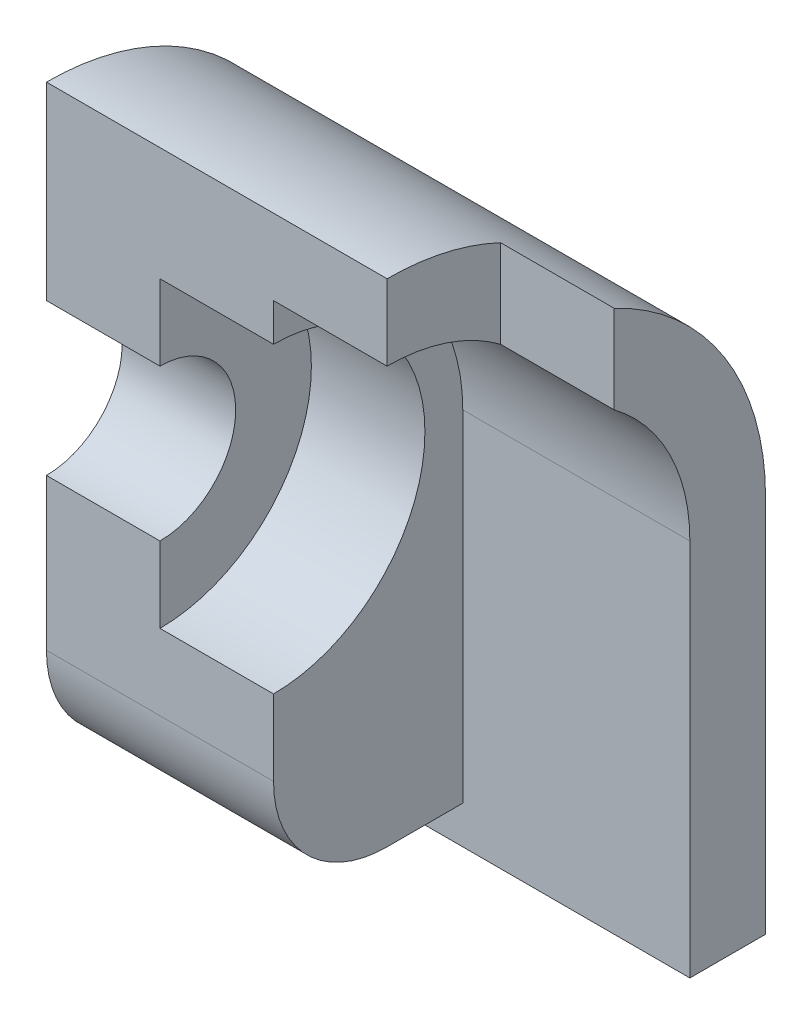
SolidWorks part; units mm, degrees
ref_plane "Front" through (0, 0, 0) normal (0, 0, 1) x (1, 0, 0)
ref_plane "Top" through (0, 0, 0) normal (0, 1, 0) x (1, 0, 0)
ref_plane "Right" through (0, 0, 0) normal (1, 0, 0) x (0, 0, -1)
sketch "Sketch1" plane through (0, 0, 0) normal (1, 0, 0) x (0, 0, -1)
  line L1 (3.5, -8) -> (-0.5, -8)
  line L2 (3.5, -8) -> (3.5, 8)
  line L3 (3.5, 8) -> (-3.5, 8)
  line L4 (-3.5, -5) -> (-3.5, 8)
  line L5 (3.5, -8) -> (-3.5, 8) construction
  line L6 (3.5, 8) -> (-3.5, -8) construction
  line L7 (3.5, -8) -> (1.5, -8)
  line L8 (3.5, -8) -> (3.5, -9)
  line L9 (3.5, -9) -> (1.5, -9)
  line L10 (1.5, -8) -> (1.5, -9)
  arc A0 (-0.5, -8) -> (-3.5, -5) centre (-0.5, -5) cw
  arc A1 (-3.5, 8) -> (3.5, 1) centre (-3.5, 1) cw
  circle A2 centre (-3.5, 1) radius 2
  point P0 (0, 0)
  dimension "D5" = 3
  dimension "D6" = 7
  dimension "D7" = 4
  dimension "D1" = 7
  dimension "D2" = 16
  dimension "D3" = 1
  dimension "D4" = 2
extrude "Boss-Extrude1" add sketch "Sketch1" along normal blind 12 contours A2 L4 A0 L1 L2 A1 | L1 L10 L9 L8
sketch "Sketch2" plane through (0, -9, 0) normal (0, -1, 0) x (1, 0, 0)
  line L0 (12, 0.5) -> (0, 0.5) construction
  line L1 (12, 3.5) -> (9, 3.5)
  line L2 (12, 3.5) -> (12, 0.5)
  line L3 (12, 0.5) -> (9, 0.5)
  line L4 (9, 3.5) -> (9, 0.5)
  dimension "D1" = 3
extrude "Cut-Extrude1" cut sketch "Sketch2" against normal blind 22
sketch "Sketch3" plane through (12, 0, 0) normal (1, 0, 0) x (0, 0, -1)
  line L0 (-3.5, 1) -> (-3.5, -8.779) construction
  line L1 (1.5, 1) -> (1.5, -8.779)
  line L2 (-8.5, 1) -> (-8.5, -8.779)
  arc A0 (1.5, 1) -> (-8.5, 1) centre (-3.5, 1) ccw
  arc A1 (-8.5, -8.779) -> (1.5, -8.779) centre (-3.5, -8.779) ccw
  point P3 (-3.5, -3.8895)
  dimension "D1" = 5
extrude "Cut-Extrude2" cut sketch "Sketch3" against normal blind 6
sketch "Sketch4" plane through (6, 0, 0) normal (1, 0, 0) x (0, 0, -1)
  circle A0 centre (-3.5, 1) radius 4
extrude "Cut-Extrude3" cut sketch "Sketch4" against normal blind 3
